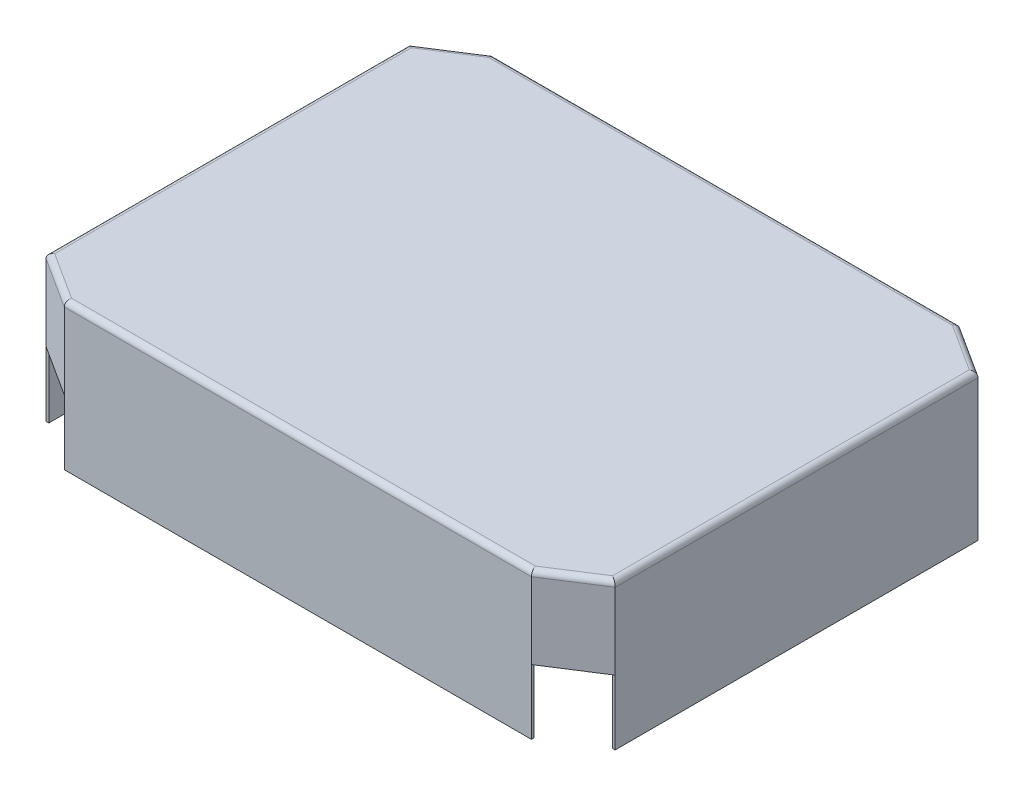
SolidWorks part; units mm, degrees
material "Thornel Mat VMA"
ref_plane "Front Plane" through (0, 0, 0) normal (0, 0, 1) x (1, 0, 0)
ref_plane "Top Plane" through (0, 0, 0) normal (0, 1, 0) x (1, 0, 0)
ref_plane "Right Plane" through (0, 0, 0) normal (1, 0, 0) x (0, 0, -1)
sketch "Sketch1" plane through (0, 0, 0) normal (0, 1, 0) x (1, 0, 0)
  line L0 (-127, 81.7796) -> (-105.2784, 95.25)
  line L1 (-127, -95.25) -> (127, -95.25)
  line L2 (-127, -95.25) -> (-127, 95.25)
  line L3 (-127, 95.25) -> (127, 95.25)
  line L4 (127, -95.25) -> (127, 95.25)
  line L5 (-70.221, 76.7042) -> (-70.221, 50.7097)
  line L6 (-70.221, 50.7097) -> (-90.1802, 35)
  line L7 (-221.4174, 201.7369) -> (-90.1802, 35) construction
  line L8 (-90.1802, 35) -> (-107.95, 35)
  line L9 (-90.1802, 35) -> (-70.221, 50.7097) construction
  line L10 (-127, 95.25) -> (127, -95.25) construction
  line L11 (-127, -95.25) -> (127, 95.25) construction
  line L12 (127, 81.7796) -> (105.2784, 95.25)
  line L13 (-201.4582, 217.4466) -> (-70.221, 50.7097) construction
  line L14 (90.1802, 35) -> (107.95, 35)
  line L15 (70.221, 76.7042) -> (70.221, 50.7097)
  line L16 (70.221, 50.7097) -> (90.1802, 35)
  line L17 (90.1802, -35) -> (107.95, -35)
  line L18 (127, -81.7796) -> (105.2784, -95.25)
  line L19 (70.221, -50.7097) -> (90.1802, -35)
  line L20 (70.221, -76.7042) -> (70.221, -50.7097)
  line L21 (-70.221, -76.7042) -> (-70.221, -50.7097)
  line L22 (16.1729, 0) -> (-27.494, 0) construction
  line L23 (0, -22.143) -> (0, 25.6257) construction
  line L25 (-90.1802, -35) -> (-107.95, -35)
  line L26 (-70.221, -50.7097) -> (-90.1802, -35)
  line L27 (-127, -81.7796) -> (-105.2784, -95.25)
  line L28 (-105.2784, 95.25) -> (105.2784, 95.25)
  line L29 (-105.2784, 95.25) -> (105.2784, 95.25)
  line L30 (-105.2784, 95.25) -> (-105.2784, 96.52)
  line L31 (-105.2784, 96.52) -> (105.2784, 96.52)
  line L32 (105.2784, 95.25) -> (105.2784, 96.52)
  line L33 (127, 81.7796) -> (128.27, 81.7796)
  line L34 (127, 81.7796) -> (127, -81.7796)
  line L35 (127, -81.7796) -> (128.27, -81.7796)
  line L36 (128.27, 81.7796) -> (128.27, -81.7796)
  line L37 (105.2784, -95.25) -> (-105.2784, -95.25)
  line L38 (105.2784, -95.25) -> (105.2784, -96.52)
  line L39 (105.2784, -96.52) -> (-105.2784, -96.52)
  line L40 (-105.2784, -95.25) -> (-105.2784, -96.52)
  line L41 (-127, 81.7796) -> (-128.27, 81.7796)
  line L42 (-127, 81.7796) -> (-127, -81.7796)
  line L43 (-127, -81.7796) -> (-128.27, -81.7796)
  line L44 (-128.27, 81.7796) -> (-128.27, -81.7796)
  line L45 (-127, 81.7796) -> (-127, -81.7796)
  line L46 (-105.2784, -95.25) -> (105.2784, -95.25)
  line L47 (105.2784, -95.25) -> (-105.2784, -95.25)
  line L48 (-105.2784, -96.52) -> (105.2784, -96.52)
  line L49 (105.2784, -95.25) -> (-105.2784, -95.25)
  line L50 (-70.221, -76.7042) -> (70.221, -76.7042)
  line L53 (-70.221, 76.7042) -> (70.221, 76.7042)
  line L57 (107.95, -35) -> (107.95, 35)
  line L58 (-107.95, -35) -> (-107.95, 35)
  point P0 (0, 0)
  point P1 (0, 0)
  point P14 (0, 0)
  point P41 (0, 0)
  dimension "D1" = 190.5
  dimension "D2" = 254
  dimension "D3" = 1.27
  dimension "D4" = 1.27
  dimension "D5" = 1.27
  dimension "D6" = 1.27
extrude "Boss-Extrude1" add sketch "Sketch1" along normal blind 29.21 contours L1 L40 L39 L38 | L41 L44 L43 L2 | L3 L32 L31 L30 | L36 L33 L4 L35
ref_plane "Plane1" through (105.2784, 29.21, -96.52) normal (1, 0, 0) x (0, 0, -1)
sketch "Sketch4" plane through (0, 29.21, 0) normal (0, 1, 0) x (1, 0, 0)
  line L0 (-128.27, 81.7796) -> (-105.2784, 96.52)
  line L1 (-105.2784, 96.52) -> (105.2784, 96.52)
  line L2 (105.2784, 96.52) -> (128.27, 81.7796)
  line L3 (128.27, 81.7796) -> (128.27, -81.7796)
  line L4 (128.27, -81.7796) -> (105.2784, -96.52)
  line L5 (105.2784, -96.52) -> (-105.2784, -96.52)
  line L6 (-105.2784, -96.52) -> (-128.27, -81.7796)
  line L7 (-128.27, -81.7796) -> (-128.27, 81.7796)
  line L8 (-127, 81.7796) -> (-105.2784, 95.25)
  line L9 (-105.2784, 95.25) -> (105.2784, 95.25)
  line L10 (105.2784, 95.25) -> (127, 81.7796)
  line L11 (127, 81.7796) -> (127, -81.7796)
  line L12 (127, -81.7796) -> (105.2784, -95.25)
  line L13 (105.2784, -95.25) -> (-105.2784, -95.25)
  line L14 (-105.2784, -95.25) -> (-127, -81.7796)
  line L15 (-127, -81.7796) -> (-127, 81.7796)
extrude "Boss-Extrude2" add sketch "Sketch4" along normal blind 35.56
sketch "Sketch5" plane through (0, 64.77, 0) normal (0, 1, 0) x (1, 0, 0)
  line L0 (-128.27, 81.7796) -> (-105.2784, 96.52)
  line L1 (-105.2784, 96.52) -> (105.2784, 96.52)
  line L2 (105.2784, 96.52) -> (128.27, 81.7796)
  line L3 (128.27, 81.7796) -> (128.27, -81.7796)
  line L4 (128.27, -81.7796) -> (105.2784, -96.52)
  line L5 (105.2784, -96.52) -> (-105.2784, -96.52)
  line L6 (-105.2784, -96.52) -> (-128.27, -81.7796)
  line L7 (-128.27, -81.7796) -> (-128.27, 81.7796)
extrude "Boss-Extrude3" add sketch "Sketch5" along normal blind 1.27
fillet "Fillet1" radius 2.54 8 edges at (-116.7742, 66.04, 89.1498) (0, 66.04, 96.52) (116.7742, 66.04, 89.1498) (128.27, 66.04, 0) (116.7742, 66.04, -89.1498) (0, 66.04, -96.52) (-128.27, 66.04, 0) (-116.7742, 66.04, -89.1498)
